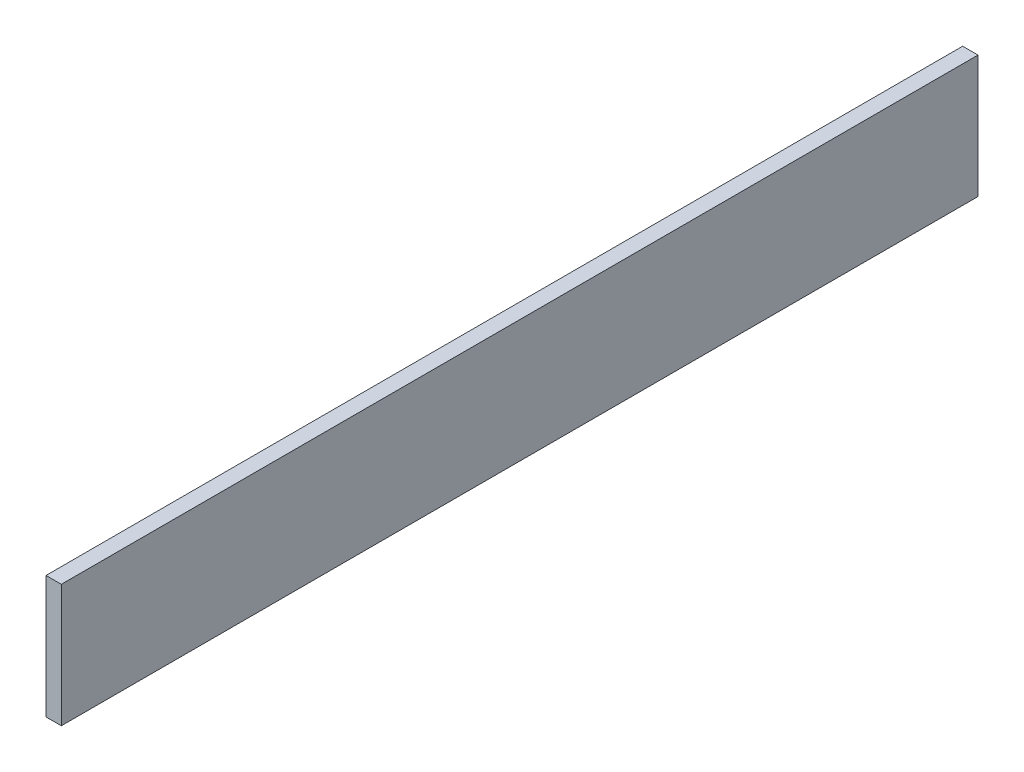
SolidWorks part; units mm, degrees
ref_plane "Front Plane" through (0, 0, 0) normal (0, 0, 1) x (1, 0, 0)
ref_plane "Top Plane" through (0, 0, 0) normal (0, 1, 0) x (1, 0, 0)
ref_plane "Right Plane" through (0, 0, 0) normal (1, 0, 0) x (0, 0, -1)
sketch "Sketch1" plane through (0, 0, 0) normal (1, 0, 0) x (0, 0, -1)
  line L1 (-1.0931, 11.595) -> (188.8989, 11.595)
  line L2 (-1.0931, 11.595) -> (-1.0931, -13.805)
  line L3 (-1.0931, -13.805) -> (188.8989, -13.805)
  line L4 (188.8989, 11.595) -> (188.8989, -13.805)
  dimension "D1" = 189.992
  dimension "D2" = 25.4
extrude "Boss-Extrude2" add sketch "Sketch1" along normal blind 3.175
